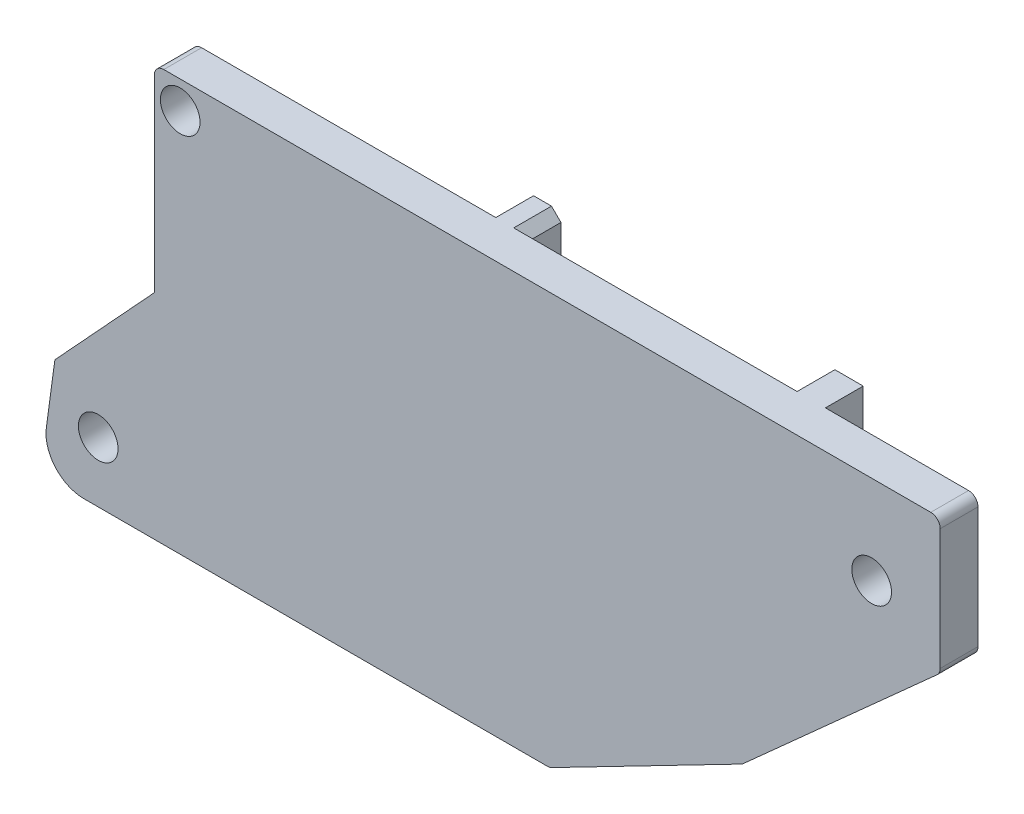
SolidWorks part; units mm, degrees
ref_plane "Plan de face" through (0, 0, 0) normal (0, 0, 1) x (1, 0, 0)
ref_plane "Plan de dessus" through (0, 0, 0) normal (0, 1, 0) x (1, 0, 0)
ref_plane "Plan de droite" through (0, 0, 0) normal (1, 0, 0) x (0, 0, -1)
sketch "Esquisse1" plane through (0, 0, 0) normal (0, 0, 1) x (1, 0, 0)
  line L0 (-20.8, 10.895) -> (20.8, -10.895) construction
  line L1 (-20.8, 10.895) -> (20.8, 10.895)
  line L2 (-20.8, 10.895) -> (-20.8, 0.4158)
  line L3 (-20.8, -10.895) -> (0.1279, -10.895)
  line L4 (20.8, 10.895) -> (20.8, 3.7654)
  line L5 (-20.8, 0.4158) -> (-26.0656, -5.2936)
  line L6 (-26.0656, -5.2936) -> (-26.8256, -10.895)
  line L7 (-26.8256, -10.895) -> (-20.8, -10.895)
  line L8 (0.1279, -10.895) -> (10.3241, -5.6331)
  line L9 (10.3241, -5.6331) -> (20.8, 3.7654)
  circle A0 centre (17.17, 6.195) radius 1.05
  circle A1 centre (-19.43, 9.435) radius 1.05
  circle A2 centre (-23.7709, -7.705) radius 1.05
  point P8 (0, 0)
  point P18 (0, 0)
  point P19 (0, 0)
  dimension "D6" = 2.1
  dimension "D1" = 41.6
  dimension "D2" = 3.63
  dimension "D3" = 4.7
  dimension "D4" = 36.6
  dimension "D5" = 3.24
  dimension "D7" = 21.79
  dimension "D8" = 17.14
  dimension "D9" = 4.3409
extrude "Boss.-Extru.1" add sketch "Esquisse1" along normal blind 2
fillet "Congé1" radius 2 1 edges at (-26.8256, -10.895, 1)
fillet "Congé2" radius 0.5 5 edges at (-20.8, 10.895, 1) (0.1279, -10.895, 1) (10.3241, -5.6331, 1) (20.8, 3.7654, 1) (20.8, 10.895, 1)
sketch "Esquisse2" plane through (0, 0, 0) normal (0, 0, -1) x (-1, 0, 0)
  line L0 (-10.7233, 9.3735) -> (3.2767, -4.635) construction
  line L2 (-10.7233, 9.3735) -> (-10.7233, -4.635)
  line L3 (-10.7233, -4.635) -> (3.2767, -4.635)
  line L4 (3.2767, 9.365) -> (3.2767, -4.635)
  line L6 (5.2267, 6.495) -> (5.2267, -7.505)
  line L7 (5.2267, -7.505) -> (19.2267, -7.505)
  line L8 (19.2267, 6.495) -> (19.2267, -7.505)
  line L9 (5.2267, 6.495) -> (19.2267, -7.505) construction
  line L10 (-10.7233, -4.635) -> (3.2767, 9.365) construction
  line L12 (-12.7233, 10.895) -> (-12.7233, -3.4806)
  line L13 (-20.3, 10.895) -> (20.3, 10.895) construction
  line L14 (-10.3718, -5.5903) -> (-20.6339, 3.6163) construction
  line L15 (-12.7233, -3.4806) -> (-10.3718, -5.5903)
  line L16 (-10.3718, -5.5903) -> (-8.3826, -6.635)
  line L17 (-0.2358, -10.8393) -> (-10.2672, -5.6624) construction
  line L18 (-8.3826, -6.635) -> (1.5283, -6.635)
  line L19 (1.5283, -6.635) -> (4.3983, -9.505)
  line L20 (4.3983, -9.505) -> (20.8, -9.505)
  line L21 (20.8, -9.505) -> (20.8, 6.495)
  line L22 (20.8, 10.395) -> (20.8, 0.4158) construction
  line L23 (20.8, 6.495) -> (19.2267, 6.495)
  line L25 (5.2267, 6.495) -> (5.2267, 10.895)
  line L26 (5.2267, 10.895) -> (3.2767, 10.895)
  line L27 (3.2767, 10.895) -> (3.2767, 9.365)
  line L28 (-10.7233, 9.3735) -> (-10.7233, 10.895)
  line L29 (-10.7233, 10.895) -> (-12.7233, 10.895)
  line L30 (-20.8, 3.9885) -> (-20.8, 10.395) construction
  point P27 (-11.7233, 10.895)
  point P32 (20.8876, 6.1474)
  point P33 (0, 0)
  dimension "D1" = 14
  dimension "D2" = 18.4
  dimension "D3" = 14
  dimension "D4" = 14
  dimension "D5" = 15.53
  dimension "D6" = 10.0767
  dimension "D7" = 1.95
  dimension "D8" = 2
  dimension "D9" = 225
  dimension "D10" = 2
  dimension "D11" = 2
  dimension "D12" = 2
extrude "Boss.-Extru.2" add sketch "Esquisse2" along normal blind 2 contours L2 L3 L4 L27 L26 L25 L6 L7 L8 L23 L21 L20 L19 L18 L16 L15 L12 L29 L28
chamfer "Chanfrein1" distance 0.5 angle 45 8 edges at (10.7233, 10.895, -1) (-3.2767, 10.895, -1) (-5.2267, 10.895, -1) (-19.2267, 6.495, -1) (-19.2267, -7.505, -1) (-5.2267, -7.505, -1) (-3.2767, -4.635, -1) (10.7233, -4.635, -1)
